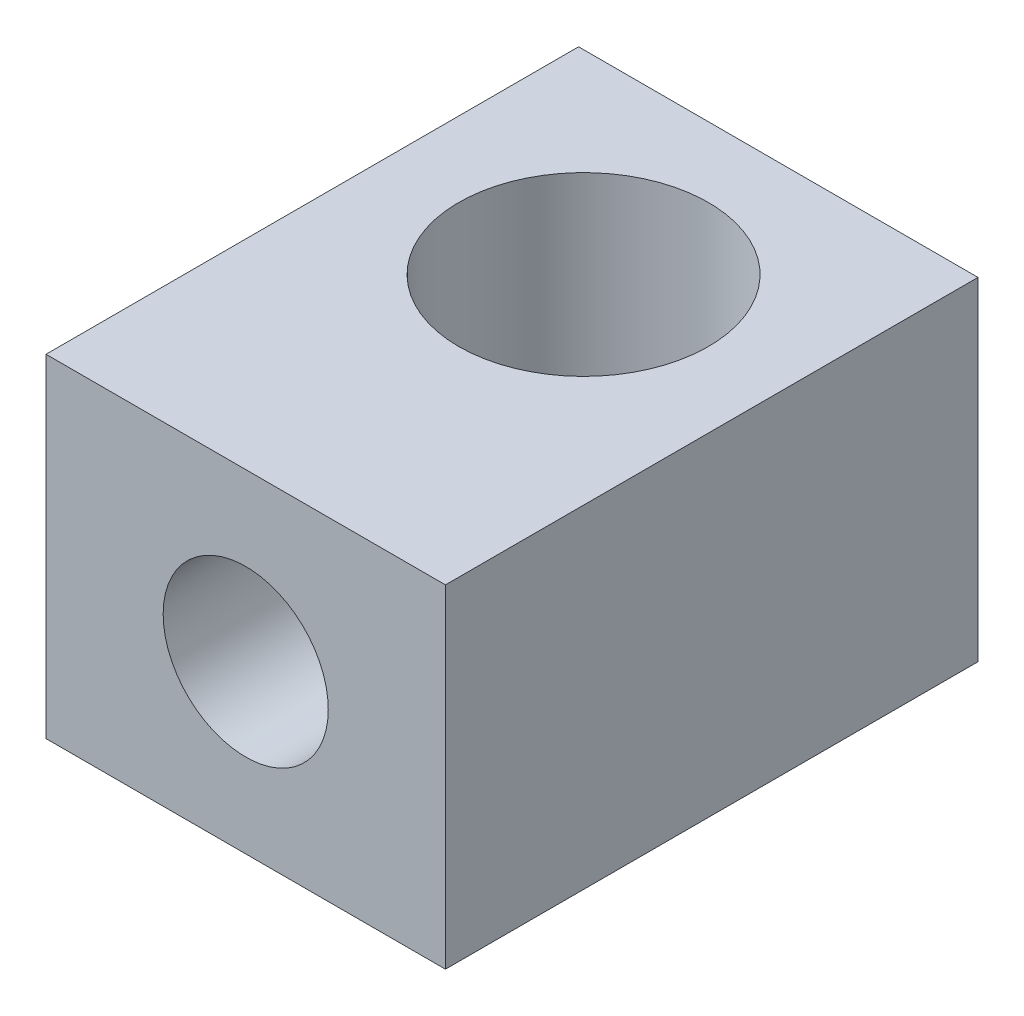
SolidWorks part; units mm, degrees
material "Pine"
ref_plane "Front Plane" through (0, 0, 0) normal (0, 0, 1) x (1, 0, 0)
ref_plane "Top Plane" through (0, 0, 0) normal (0, 1, 0) x (1, 0, 0)
ref_plane "Right Plane" through (0, 0, 0) normal (1, 0, 0) x (0, 0, -1)
sketch "Sketch1" plane through (0, 0, 0) normal (0, 1, 0) x (1, 0, 0)
  line L0 (0, 0) -> (60, 0)
  line L1 (60, 0) -> (60, 80)
  line L2 (60, 80) -> (0, 80)
  line L3 (0, 80) -> (0, 0)
  circle A0 centre (30, 50.75) radius 18.75
  point P7 (0, 0)
  dimension "D3" = 37.5
  dimension "D1" = 80
  dimension "D2" = 60
  dimension "D4" = 50.75
  dimension "D5" = 30
extrude "Boss-Extrude1" add sketch "Sketch1" along normal mid plane 50
ref_plane "Plane1" through (0, 0, -50.75) normal (0, 0, 1) x (1, 0, 0)
sketch "Sketch4" plane through (0, 0, -50.75) normal (0, 0, 1) x (1, 0, 0)
  line L0 (0, 25) -> (0, -25) construction
  line L1 (0, 25) -> (0, -25)
  line L2 (0, 25) -> (60, 25) construction
  line L3 (0, 25) -> (60, 25)
  circle A0 centre (30, 0) radius 12.4
  dimension "D1" = 24.8
  dimension "D2" = 30
  dimension "D3" = 25
extrude "Cut-Extrude1" cut sketch "Sketch4" along normal through all contours A0
